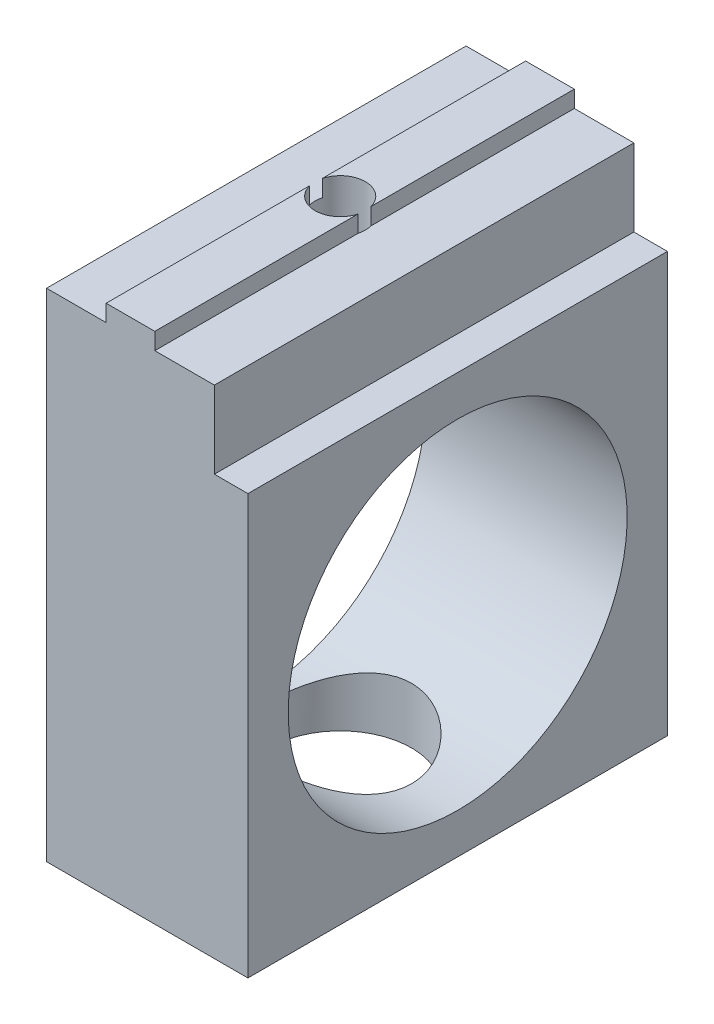
SolidWorks part; units mm, degrees
ref_plane "Front Plane" through (0, 0, 0) normal (0, 0, 1) x (1, 0, 0)
ref_plane "Top Plane" through (0, 0, 0) normal (0, 1, 0) x (1, 0, 0)
ref_plane "Right Plane" through (0, 0, 0) normal (1, 0, 0) x (0, 0, -1)
sketch "Sketch1" plane through (0, 0, 0) normal (0, 0, 1) x (1, 0, 0)
  line L0 (-5, 0) -> (5, 0)
  line L1 (5, 0) -> (5, 7)
  line L2 (5, 7) -> (1.45, 7)
  line L3 (1.45, 7) -> (1.45, 8)
  line L4 (1.45, 8) -> (-1.45, 8)
  line L5 (-1.45, 8) -> (-1.45, 7)
  line L6 (-1.45, 7) -> (-5, 7)
  line L7 (-5, 7) -> (-5, 0)
  point P9 (0, 0)
  dimension "D1" = 10
  dimension "D2" = 2.9
  dimension "D3" = 7
  dimension "D4" = 1
extrude "MakerBeamFix" add sketch "Sketch1" along normal mid plane 25
sketch "Sketch3" plane through (-5, 0, 0) normal (-1, 0, 0) x (0, 0, 1)
  line L1 (12.5, -22.6) -> (-12.5, -22.6)
  line L2 (12.5, -22.6) -> (12.5, 2.4)
  line L3 (12.5, 2.4) -> (-12.5, 2.4)
  line L4 (-12.5, -22.6) -> (-12.5, 2.4)
  line L5 (12.5, -22.6) -> (-12.5, 2.4) construction
  line L6 (12.5, 2.4) -> (-12.5, -22.6) construction
  line L9 (12.5, 0) -> (-12.5, 0) construction
  line L10 (-12.5, 7) -> (-12.5, 0) construction
  circle A0 centre (0, -10.1) radius 10.1
  point P6 (-15, 3.5)
  point P9 (19.5947, 4.563)
  point P10 (-15, 4.4317)
  point P13 (10.3841, 2.9808)
  dimension "D1" = 20.2
  dimension "D2" = 25
  dimension "D3" = 25
extrude "MakerBeamThreadingTap" add sketch "Sketch3" against normal blind 12
sketch "Sketch4" plane through (0, -22.6, 0) normal (0, -1, 0) x (1, 0, 0)
  line L0 (-5, -12.5) -> (-5, 12.5) construction
  circle A0 centre (0, 0) radius 1.5
  point P4 (0, 0)
  point P5 (-5, 0)
  dimension "D1" = 3
  dimension "D2" = 5
extrude "FixingHole" cut sketch "Sketch4" against normal through all
ref_plane "Plane1" through (0, 4, 0) normal (0, 1, 0) x (1, 0, 0)
sketch "Sketch5" plane through (0, 4, 0) normal (0, 1, 0) x (1, 0, 0)
  circle A0 centre (0, 0) radius 4.25
  dimension "D1" = 8.5
extrude "DriverHole" cut sketch "Sketch5" against normal through all
